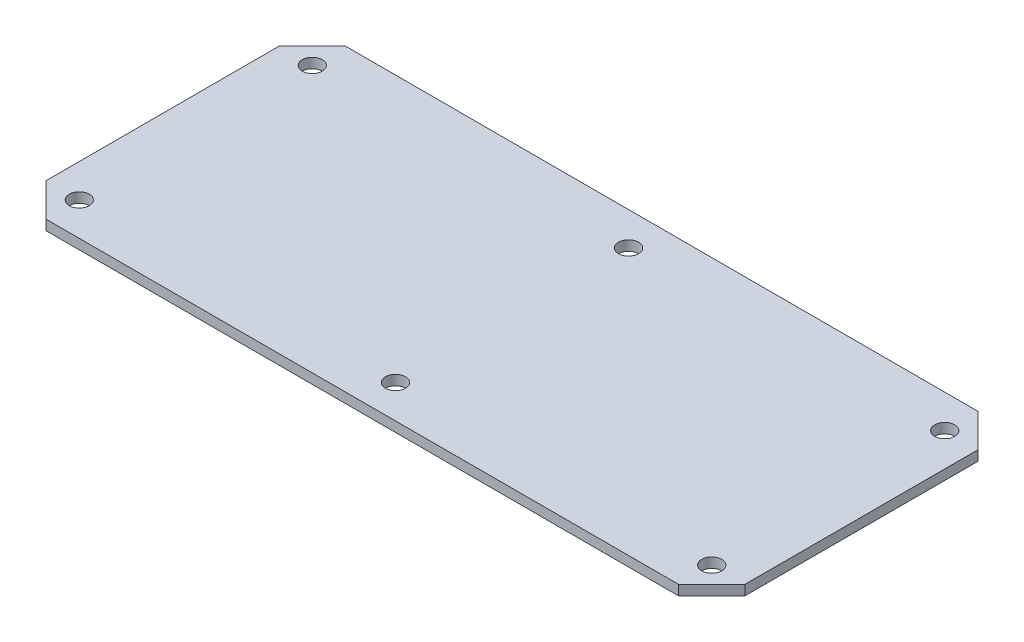
SolidWorks part; units mm, degrees
ref_plane "Plan de face" through (0, 0, 0) normal (0, 0, 1) x (1, 0, 0)
ref_plane "Plan de dessus" through (0, 0, 0) normal (0, 1, 0) x (1, 0, 0)
ref_plane "Plan de droite" through (0, 0, 0) normal (1, 0, 0) x (0, 0, -1)
sketch "Esquisse1" plane through (0, 0, 0) normal (0, 1, 0) x (1, 0, 0)
  line L0 (0, 45) -> (210, 45) construction
  line L1 (210, 90) -> (0, 90)
  line L2 (210, 90) -> (210, 0)
  line L3 (210, 0) -> (0, 0)
  line L4 (0, 90) -> (0, 0)
  line L6 (105, 90) -> (105, 0) construction
  line L7 (200, 10) -> (10, 10) construction
  line L8 (200, 10) -> (200, 80) construction
  line L9 (200, 80) -> (10, 80) construction
  line L10 (10, 10) -> (10, 80) construction
  line L11 (200, 10) -> (10, 80) construction
  line L12 (200, 80) -> (10, 10) construction
  point P7 (105, 45)
  dimension "D1" = 210
  dimension "D2" = 90
  dimension "D3" = 190
  dimension "D4" = 70
extrude "Boss.-Extru.1" add sketch "Esquisse1" along normal blind 3
sketch "Esquisse2" plane through (0, 3, 0) normal (0, 1, 0) x (1, 0, 0)
  line L0 (200, 80) -> (10, 80) construction
  line L1 (200, 10) -> (10, 10) construction
  circle A0 centre (10, 80) radius 3
  circle A1 centre (105, 80) radius 3
  circle A2 centre (200, 80) radius 3
  circle A3 centre (200, 10) radius 3
  circle A4 centre (105, 10) radius 3
  circle A5 centre (10, 10) radius 3
  dimension "D1" = 6
extrude "Enlèv. mat.-Extru.1" cut sketch "Esquisse2" against normal blind 3
chamfer "Chamfer1" distance 10 angle 45 4 edges at (210, 1.5, 0) (210, 1.5, -90) (0, 1.5, 0) (0, 1.5, -90)
